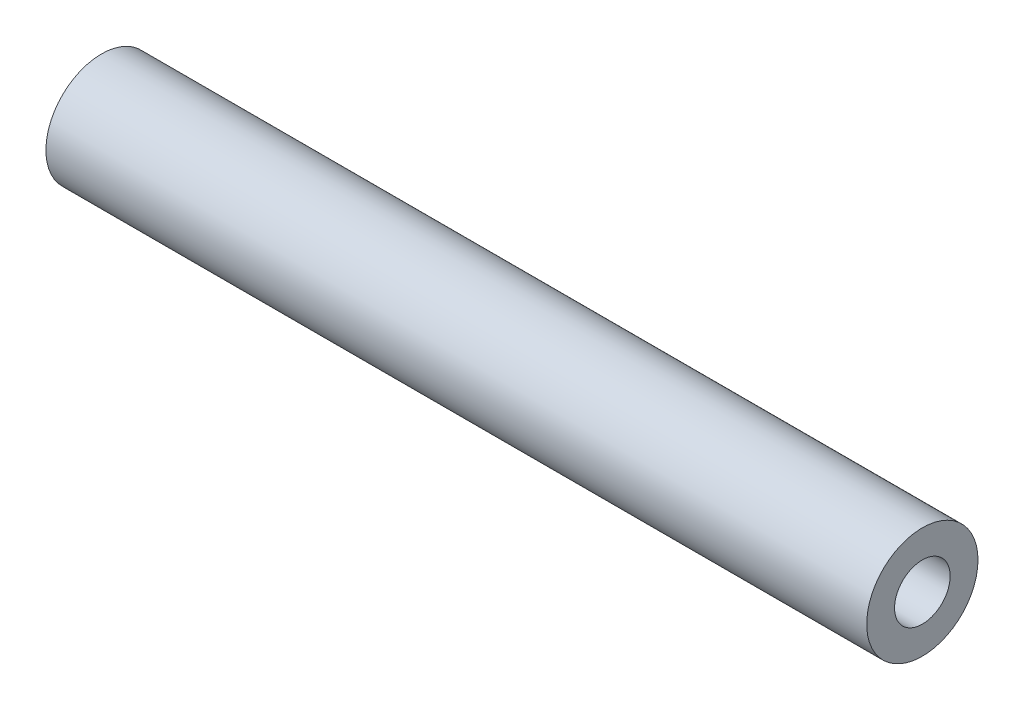
SolidWorks part; units mm, degrees
material "6061-T6 (SS)"
ref_plane "Front Plane" through (0, 0, 0) normal (0, 0, 1) x (1, 0, 0)
ref_plane "Top Plane" through (0, 0, 0) normal (0, 1, 0) x (1, 0, 0)
ref_plane "Right Plane" through (0, 0, 0) normal (1, 0, 0) x (0, 0, -1)
sketch "Sketch1" plane through (0, 0, 0) normal (1, 0, 0) x (0, 0, -1)
  circle A0 centre (0, 0) radius 6.35
  circle A1 centre (0, 0) radius 12.7
  dimension "D1" = 12.7
  dimension "D2" = 25.4
extrude "Boss-Extrude1" add sketch "Sketch1" along normal mid plane 187.325
